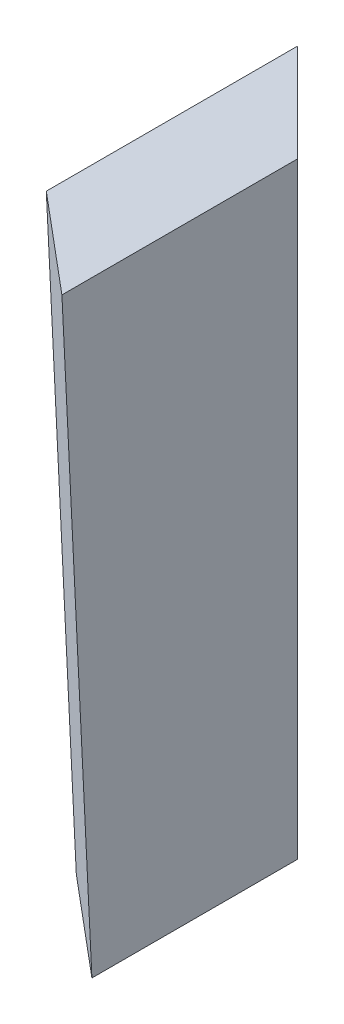
SolidWorks part; units mm, degrees
ref_plane "Alzado" through (0, 0, 0) normal (0, 0, 1) x (1, 0, 0)
ref_plane "Planta" through (0, 0, 0) normal (0, 1, 0) x (1, 0, 0)
ref_plane "Vista lateral" through (0, 0, 0) normal (1, 0, 0) x (0, 0, -1)
sketch "Croquis1" plane through (0, 0, 0) normal (0, 1, 0) x (1, 0, 0)
  line L0 (12.4958, -38.8275) -> (0, -28.33)
  line L1 (0, -28.33) -> (0, 0)
  line L2 (0, 0) -> (12.4958, -12.5075)
  line L3 (12.4958, -12.5075) -> (12.4958, -38.8275)
  point P5 (0, 0)
  dimension "D1" = 17.68
  dimension "D2" = 28.33
  dimension "D3" = 16.32
  dimension "D4" = 26.32
ref_plane "Plano1" through (0, 75, 0) normal (0, 1, 0) x (1, 0, 0)
sketch "Croquis2" plane through (0, 75, 0) normal (0, 1, 0) x (1, 0, 0)
  line L0 (9.8758, -9.8875) -> (-2.62, 2.62)
  line L2 (-2.62, 2.62) -> (-2.62, -29.55)
  line L3 (-2.62, -29.55) -> (9.8758, -40.0475)
  line L4 (9.8758, -40.0475) -> (9.8758, -9.8875)
  line L5 (12.4958, -12.5075) -> (9.8758, -12.5075)
  line L6 (9.8758, -12.5075) -> (9.8758, -9.8875)
  point P3 (0, 0)
  dimension "D1" = 17.68
  dimension "D2" = 16.32
  dimension "D3" = 30.16
  dimension "D4" = 32.17
  dimension "D5" = 2.62
  dimension "D6" = 2.62
loft "Recubrir1" add profiles "Croquis1" section "Croquis2" section "Croquis1"
